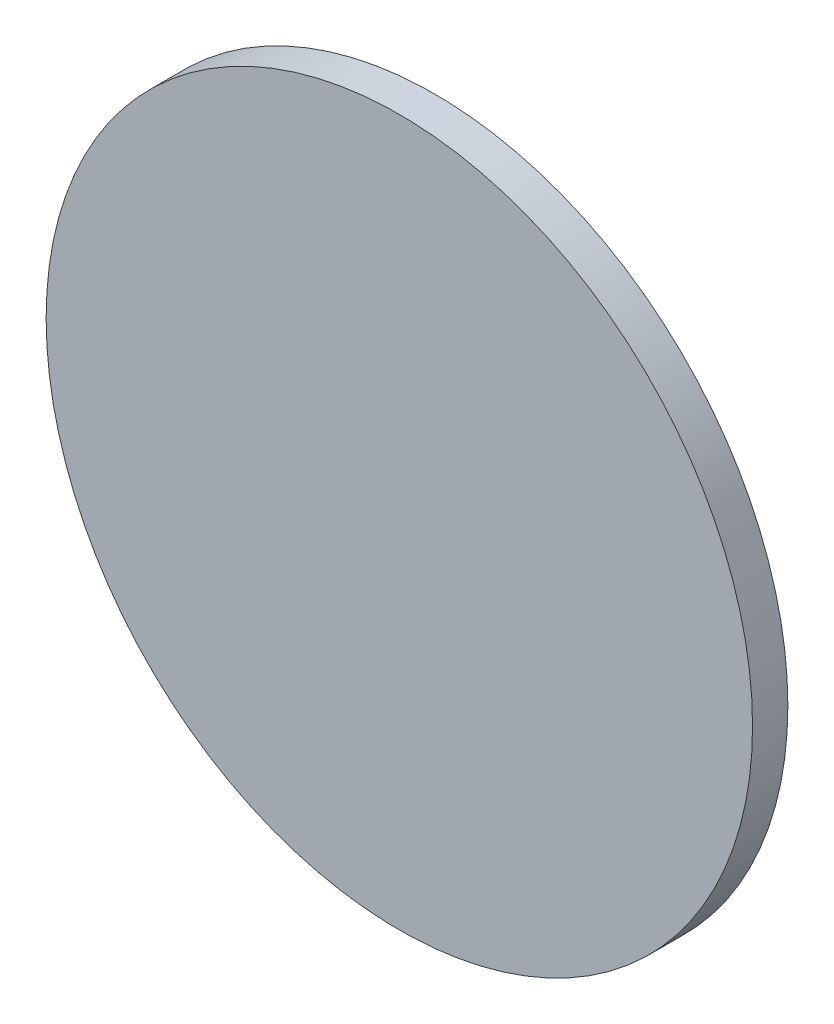
SolidWorks part; units mm, degrees
ref_plane "Front" through (0, 0, 0) normal (0, 0, 1) x (1, 0, 0)
ref_plane "Top" through (0, 0, 0) normal (0, 1, 0) x (1, 0, 0)
ref_plane "Right" through (0, 0, 0) normal (1, 0, 0) x (0, 0, -1)
sketch "Sketch1" plane through (0, 0, 0) normal (0, 0, 1) x (1, 0, 0)
  circle A0 centre (0, 0) radius 100
extrude "Boss-Extrude1" add sketch "Sketch1" along normal blind 10
